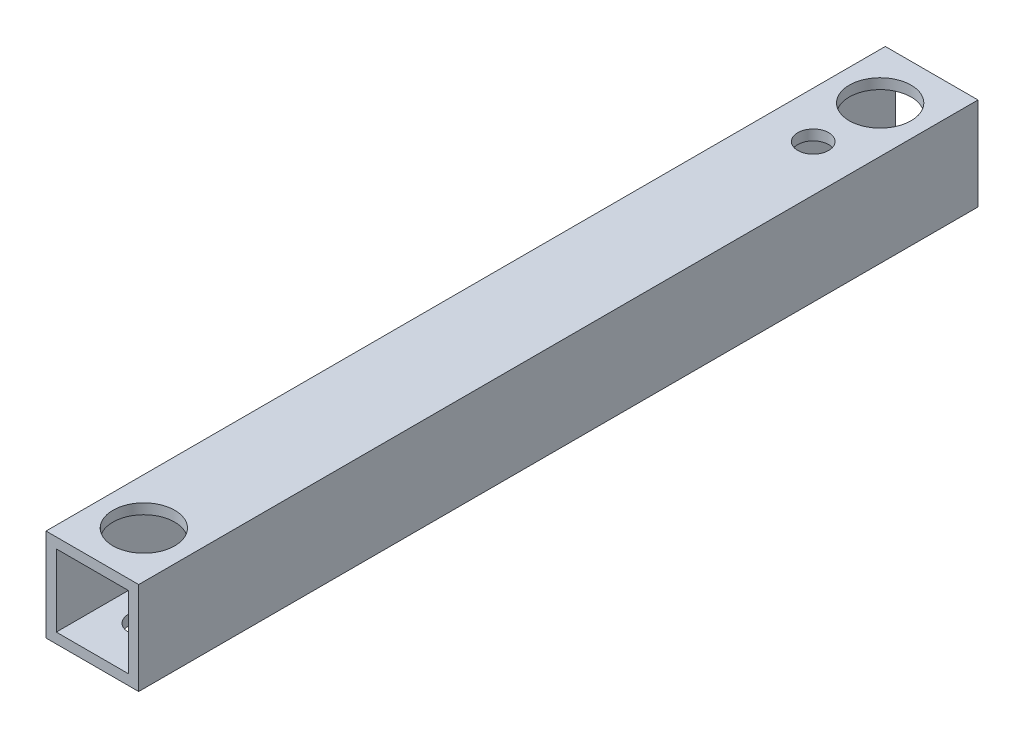
SolidWorks part; units mm, degrees
ref_plane "正面" through (0, 0, 0) normal (0, 0, 1) x (1, 0, 0)
ref_plane "平面" through (0, 0, 0) normal (0, 1, 0) x (1, 0, 0)
ref_plane "右側面" through (0, 0, 0) normal (1, 0, 0) x (0, 0, -1)
sketch "ｽｹｯﾁ1" plane through (0, 0, 0) normal (0, 0, 1) x (1, 0, 0)
  line L1 (-4.5, 4.5) -> (4.5, 4.5)
  line L2 (-4.5, 4.5) -> (-4.5, -4.5)
  line L3 (-4.5, -4.5) -> (4.5, -4.5)
  line L4 (4.5, 4.5) -> (4.5, -4.5)
  line L5 (-4.5, 4.5) -> (4.5, -4.5) construction
  line L6 (-4.5, -4.5) -> (4.5, 4.5) construction
  point P0 (0, 0)
  dimension "D1" = 9
  dimension "D2" = 9
extrude "ﾎﾞｽ - 押し出し1" add sketch "ｽｹｯﾁ1" along normal blind 81.5
sketch "ｽｹｯﾁ2" plane through (0, 0, 81.5) normal (0, 0, 1) x (1, 0, 0)
  line L1 (-3.5, 3.5) -> (3.5, 3.5)
  line L2 (-3.5, 3.5) -> (-3.5, -3.5)
  line L3 (-3.5, -3.5) -> (3.5, -3.5)
  line L4 (3.5, 3.5) -> (3.5, -3.5)
  line L5 (-3.5, 3.5) -> (3.5, -3.5) construction
  line L6 (-3.5, -3.5) -> (3.5, 3.5) construction
  point P0 (0, 0)
  dimension "D1" = 7
  dimension "D2" = 7
extrude "ｶｯﾄ - 押し出し1" cut sketch "ｽｹｯﾁ2" against normal blind 101.5
sketch "ｽｹｯﾁ3" plane through (0, 4.5, 0) normal (0, 1, 0) x (1, 0, 0)
  line L0 (0, 0) -> (0, -5)
  line L1 (4.5, 0) -> (-4.5, 0) construction
  line L2 (0, -5) -> (0, -11.5)
  line L3 (0, -11.5) -> (0, -76.5)
  circle A0 centre (0, -5) radius 3
  circle A1 centre (0, -11.5) radius 1.5
  circle A2 centre (0, -76.5) radius 1.5
  dimension "D1" = 6
  dimension "D2" = 3
  dimension "D3" = 3
  dimension "D4" = 5
  dimension "D5" = 6.5
  dimension "D6" = 65
extrude "ｶｯﾄ - 押し出し2" cut sketch "ｽｹｯﾁ3" against normal blind 111.5
sketch "ｽｹｯﾁ4" plane through (0, 4.5, 0) normal (0, 1, 0) x (1, 0, 0)
  circle A0 centre (0, -76.5) radius 3
  dimension "D1" = 6
extrude "ｶｯﾄ - 押し出し3" cut sketch "ｽｹｯﾁ4" against normal blind 1
